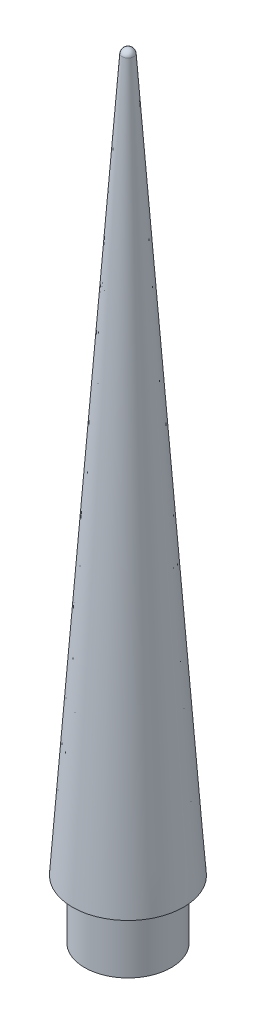
SolidWorks part; units mm, degrees
material "6061-T6 (SS)"
ref_plane "Front Plane" through (0, 0, 0) normal (0, 0, 1) x (1, 0, 0)
ref_plane "Top Plane" through (0, 0, 0) normal (0, 1, 0) x (1, 0, 0)
ref_plane "Right Plane" through (0, 0, 0) normal (1, 0, 0) x (0, 0, -1)
sketch "Sketch1" plane through (0, 0, 0) normal (0, 1, 0) x (1, 0, 0)
  circle A0 centre (0, 0) radius 9.398
  dimension "D1" = 18.796
extrude "Boss-Extrude1" add sketch "Sketch1" along normal blind 12.7
sketch "Sketch3" plane through (0, 0, 0) normal (1, 0, 0) x (0, 0, -1)
  line L0 (12.065, 12.7) -> (0, 185.2375)
  line L1 (0, 185.2375) -> (0, 12.7)
  line L2 (9.398, 12.7) -> (-9.398, 12.7) construction
  line L3 (0, 12.7) -> (12.065, 12.7)
  line L5 (0, 167.0757) -> (1.27, 167.0757) construction
  arc A0 (1.27, 167.0757) -> (0, 168.3457) centre (0, 167.0757) ccw
  point P6 (11.303, 12.7)
  point P8 (0, 0)
  point P11 (12.0642, 12.7)
  dimension "D1" = 1.27
  dimension "D2" = 12.065
  dimension "D3" = 86
revolve "Revolve1" add sketch "Sketch3" angle 360 about L1
sketch "Sketch5" plane through (0, 0, 0) normal (0, -1, 0) x (1, 0, 0)
  point P0 (0, 0)
hole_wizard "Tap Drill for #8-32 Tap1" positions "Sketch7" profile "Sketch9" hole size "#8-32" standard "ANSI Inch"
sketch "Sketch7" plane through (0, 0, 0) normal (0, -1, 0) x (-1, 0, 0)
  point P0 (0, 0)
sketch "Sketch9" plane through (0, 0, 0) normal (1, 0, 0) x (0, 0, -1)
  line L0 (0, 0) -> (0, 11.1978)
  line L1 (0, 11.1978) -> (1.7272, 10.16)
  line L2 (1.7272, 10.16) -> (1.7272, 0)
  line L5 (1.7272, 0) -> (0, 0)
  line L10 (0, 11.1978) -> (-1.7272, 10.16) construction
  line L11 (0, -6.35) -> (0, 107.95) construction
  dimension "Hole Dia." = 3.4544
  dimension "Hole Depth" = 10.16
  dimension "Drill Angle" = 118
